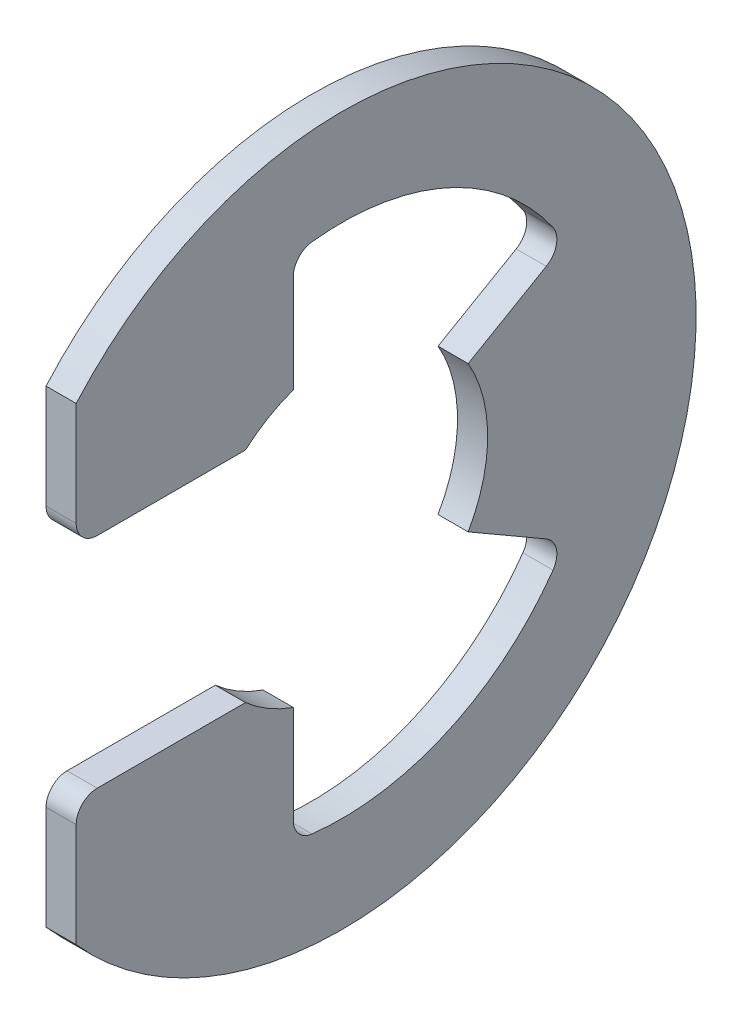
SolidWorks part; units mm, degrees
material "Plain Carbon Steel"
ref_plane "Front" through (0, 0, 0) normal (0, 0, 1) x (1, 0, 0)
ref_plane "Top" through (0, 0, 0) normal (0, 1, 0) x (1, 0, 0)
ref_plane "Right" through (0, 0, 0) normal (1, 0, 0) x (0, 0, -1)
sketch "Sketch1" plane through (0, 0, 0) normal (1, 0, 0) x (0, 0, -1)
  line L0 (-2.0329, 2.3051) -> (-5.6007, 2.305)
  line L1 (-5.6007, 4.9394) -> (-5.6007, 2.305)
  line L2 (-5.6007, -4.9394) -> (-5.6007, -2.3051)
  line L3 (-5.6007, -2.3051) -> (-2.0329, -2.3051)
  line L4 (2.6616, -1.5367) -> (4.7116, -2.7203)
  line L5 (2.6616, 1.5367) -> (4.7116, 2.7203)
  line L6 (0, 0) -> (-7.747, 0) construction
  line L7 (2.6616, 1.5367) -> (2.6616, -1.5367) construction
  line L8 (-1.0245, -2.8976) -> (-1.0245, -5.3432)
  line L9 (0, 7.4676) -> (0, -7.4676) construction
  line L10 (-1.0245, 5.3432) -> (-1.0245, 2.8976)
  circle A1 centre (0, 0) radius 7.747 construction
  circle A2 centre (0, 0) radius 3.0734 construction
  arc A3 (-5.6007, -4.9394) -> (-5.6007, 4.9394) centre (0, 0) ccw
  arc A4 (-2.0329, -2.3051) -> (-1.0245, -2.8976) centre (0, 0) ccw
  arc A5 (-2.0329, 2.3051) -> (-1.0245, 2.8976) centre (0, 0) cw
  arc A6 (2.6616, 1.5367) -> (2.6616, -1.5367) centre (0, 0) cw
  arc A7 (-1.0245, -5.3432) -> (4.7116, -2.7203) centre (0, 0) ccw
  arc A8 (4.7116, 2.7203) -> (-1.0245, 5.3432) centre (0, 0) ccw
  dimension "D1" = 5.4405
  dimension "OD" = 14.9352
  dimension "L" = 15.494
  dimension "D" = 6.1468
  dimension "D5" = 1.0245
  dimension "D2" = 60
  dimension "D3" = 4.6101
  dimension "D4" = 13.0683
extrude "Extrude1" add sketch "Sketch1" along normal mid plane 0.635
fillet "Fillet1" radius 0.4445 6 edges at (0, -2.7203, -4.7116) (0, 2.7203, -4.7116) (0, -2.3051, 5.6007) (0, -5.3432, 1.0245) (0, 2.305, 5.6007) (0, 5.3432, 1.0245)
sketch "Sketch3" plane through (0, 0, 0) normal (0, 1, 0) x (1, 0, 0)
  line L0 (0.3683, 3.9624) -> (0.3683, 3.175)
  line L1 (0.3683, 3.175) -> (-0.3683, 3.175)
  line L2 (-0.3683, 3.175) -> (-0.3683, 3.9624)
  line L3 (-0.3683, 3.9624) -> (-5.1562, 3.9624)
  line L4 (2.2098, 0) -> (2.2098, 3.5687)
  line L5 (-5.1562, 3.9624) -> (-5.1562, 0)
  line L6 (-5.1562, 0) -> (2.2098, 0)
  line L8 (2.2098, 0) -> (2.2098, 3.9624) construction
  line L9 (2.2098, 3.9624) -> (0.3683, 3.9624) construction
  line L10 (2.2098, 0) -> (17.2631, 0) construction
  line L11 (2.2098, 3.5687) -> (1.8161, 3.9624)
  line L12 (1.8161, 3.9624) -> (0.3683, 3.9624)
  point P2 (0, 3.175)
  point P5 (0.3683, 3.5687)
  dimension "D1" = 1.8415
  dimension "Ds" = 7.9248
  dimension "Dg" = 6.35
  dimension "W" = 0.7366
  dimension "D2" = 7.366
  dimension "D3" = 45
revolve "Revolve2" [suppressed] add sketch "Sketch3" angle 360 about L10
equation "\"D2@Sketch3\" = \"W@Sketch3\"*10"
equation "\"D1@Sketch3\" = \"D2@Sketch3\"/4"
equation "\"D1@Sketch1\" = (\"OD@Sketch1\"+\"D@Sketch1\")/3.875"
equation "\"D3@Sketch1\" = \"D@Sketch1\"*.75"
equation "\"D1@Fillet1\" = \"D1@Extrude1\"*.7"
equation "\"D4@Sketch1\" = \"OD@Sketch1\"*.875"
equation "\"D5@Sketch1\" = \"D@Sketch1\"/6"
